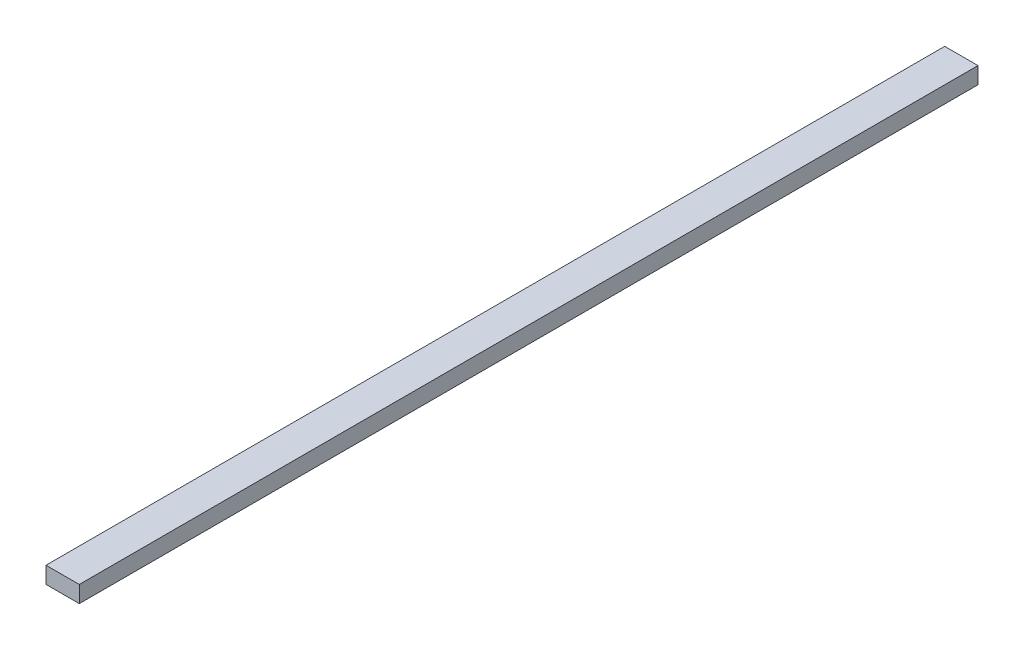
SolidWorks part; units mm, degrees
ref_plane "Front Plane" through (0, 0, 0) normal (0, 0, 1) x (1, 0, 0)
ref_plane "Top Plane" through (0, 0, 0) normal (0, 1, 0) x (1, 0, 0)
ref_plane "Right Plane" through (0, 0, 0) normal (1, 0, 0) x (0, 0, -1)
sketch "Sketch1" plane through (0, 0, 0) normal (0, 0, 1) x (1, 0, 0)
  line L0 (0, 0) -> (101.6, 0)
  line L1 (101.6, 0) -> (101.6, 50.8)
  line L2 (101.6, 50.8) -> (0, 50.8)
  line L3 (0, 50.8) -> (0, 0)
  dimension "D1" = 101.6
  dimension "D2" = 50.8
extrude "Boss-Extrude1" add sketch "Sketch1" along normal blind 2743.2
